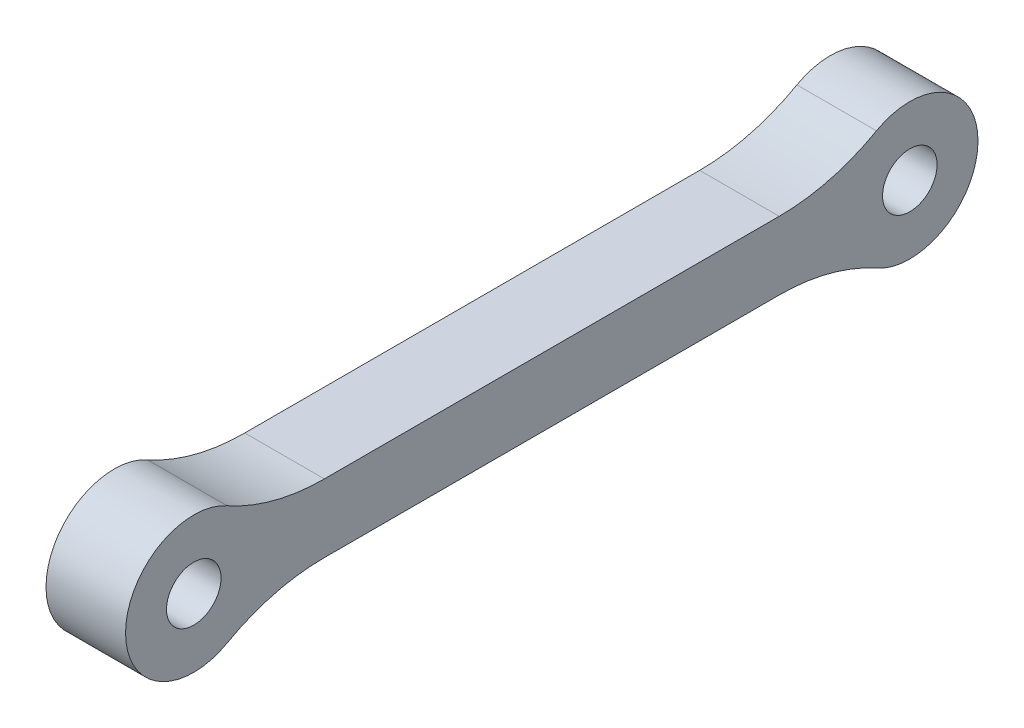
SolidWorks part; units mm, degrees
material "Tough 2000"
ref_plane "Front Plane" through (0, 0, 0) normal (0, 0, 1) x (1, 0, 0)
ref_plane "Top Plane" through (0, 0, 0) normal (0, 1, 0) x (1, 0, 0)
ref_plane "Right Plane" through (0, 0, 0) normal (1, 0, 0) x (0, 0, -1)
sketch "Sketch1" plane through (0, 0, 0) normal (1, 0, 0) x (0, 0, -1)
  line L2 (18, 1.7143) -> (33.0308, 1.7143)
  line L3 (18, 1.7143) -> (2.9692, 1.7143)
  line L5 (18, -1.7143) -> (33.0308, -1.7143)
  line L6 (18, -1.7143) -> (2.9692, -1.7143)
  arc A0 (33.0308, -1.7143) -> (33.0308, 1.7143) centre (36, 0) ccw
  arc A1 (2.9692, 1.7143) -> (2.9692, -1.7143) centre (0, 0) ccw
  circle A2 centre (0, 0) radius 1.3714
  circle A3 centre (36, 0) radius 1.3714
  dimension "D1" = 36
extrude "Boss-Extrude1" add sketch "Sketch1" along normal blind 4
fillet "Fillet1" radius 10 4 edges at (2, 1.7143, -2.9692) (2, -1.7143, -2.9692) (2, -1.7143, -33.0308) (2, 1.7143, -33.0308)
